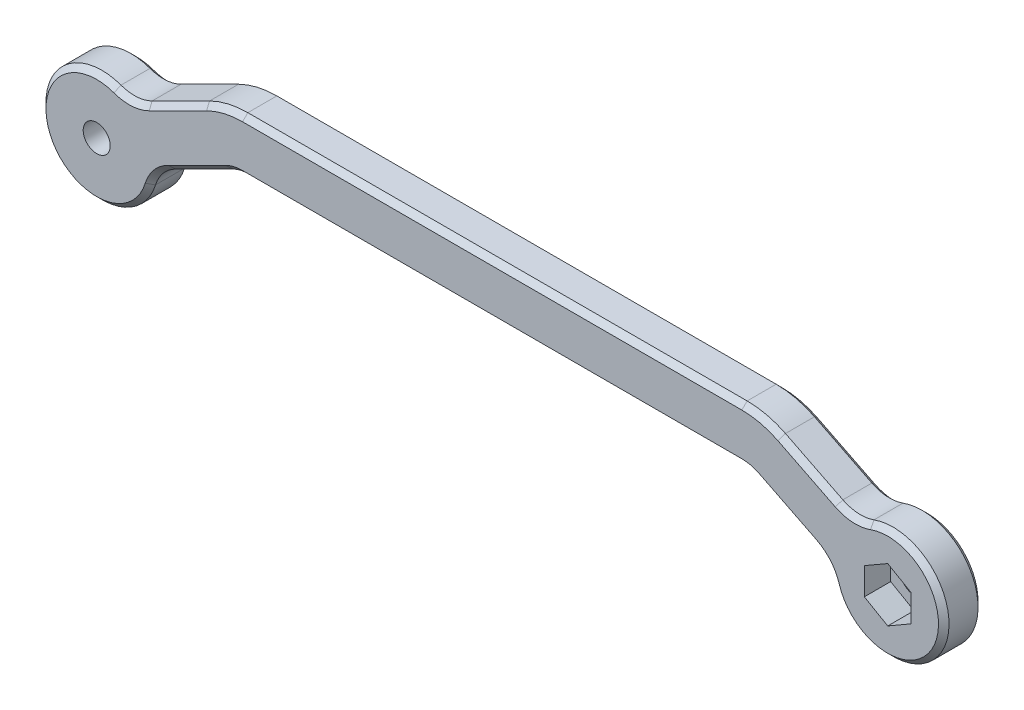
SolidWorks part; units mm, degrees
ref_plane "Front Plane" through (0, 0, 0) normal (0, 0, 1) x (1, 0, 0)
ref_plane "Top Plane" through (0, 0, 0) normal (0, 1, 0) x (1, 0, 0)
ref_plane "Right Plane" through (0, 0, 0) normal (1, 0, 0) x (0, 0, -1)
sketch "Sketch1" plane through (0, 0, 0) normal (0, 0, 1) x (1, 0, 0)
  line L0 (-60, 0) -> (60, 0) construction
  line L1 (-60, 0) -> (-40, 10) construction
  line L2 (-40, 10) -> (40, 10) construction
  line L3 (40, 10) -> (60, 0) construction
  line L4 (-40.9443, 14) -> (40.9443, 14) construction
  line L5 (40.9443, 14) -> (61.7889, 3.5777) construction
  line L6 (-61.7889, 3.5777) -> (-40.9443, 14) construction
  line L7 (-52.3974, 8.2735) -> (-43.6892, 12.6276)
  line L8 (-37.8754, 14) -> (37.8754, 14)
  line L9 (43.6892, 12.6276) -> (52.3974, 8.2735)
  line L10 (43.6892, 12.6276) -> (61.7889, 3.5777) construction
  line L11 (-37.8754, 6) -> (37.8754, 6)
  line L12 (40.1115, 5.4721) -> (48.8197, 1.118)
  line L13 (-61.7889, 3.5777) -> (-43.6892, 12.6276) construction
  line L14 (-48.8197, 1.118) -> (-40.1115, 5.4721)
  line L15 (-58.2111, -3.5777) -> (-40.1115, 5.4721) construction
  line L17 (40.1115, 5.4721) -> (58.2111, -3.5777) construction
  circle A0 centre (-60, 0) radius 2.05
  circle A1 centre (60, 0) radius 2.05
  arc A2 (-57.1162, 7.9959) -> (-51.873, -2.4905) centre (-60, 0) ccw
  arc A3 (51.873, -2.4905) -> (57.1162, 7.9959) centre (60, 0) ccw
  arc A4 (37.8754, 14) -> (43.6892, 12.6276) centre (37.8754, 1) cw
  arc A5 (-43.6892, 12.6276) -> (-37.8754, 14) centre (-37.8754, 1) cw
  arc A6 (-40.1115, 5.4721) -> (-37.8754, 6) centre (-37.8754, 1) cw
  arc A7 (37.8754, 6) -> (40.1115, 5.4721) centre (37.8754, 1) cw
  arc A8 (-52.3974, 8.2735) -> (-57.1162, 7.9959) centre (-55.0807, 13.64) cw
  arc A9 (52.3974, 8.2735) -> (57.1162, 7.9959) centre (55.0807, 13.64) ccw
  arc A10 (48.8197, 1.118) -> (51.873, -2.4905) centre (46.1364, -4.2485) cw
  arc A11 (-51.873, -2.4905) -> (-48.8197, 1.118) centre (-46.1364, -4.2485) cw
  point P4 (0, 0)
  point P9 (0, 10)
  dimension "D1" = 4.1
  dimension "D2" = 4.1
  dimension "D3" = 17
  dimension "D4" = 17
  dimension "D8" = 13
  dimension "D11" = 6
  dimension "D12" = 8
  dimension "D10" = 6
  dimension "D5" = 120
  dimension "D6" = 80
  dimension "D7" = 10
  dimension "D9" = 4
extrude "Boss-Extrude1" add sketch "Sketch1" along normal blind 6
sketch "Sketch3" plane through (0, 0, 6) normal (0, 0, 1) x (1, 0, 0)
  line L7 (60, 4.0992) -> (56.45, 2.0496)
  line L8 (56.45, 2.0496) -> (56.45, -2.0496)
  line L9 (56.45, -2.0496) -> (60, -4.0992)
  line L10 (60, -4.0992) -> (63.55, -2.0496)
  line L11 (63.55, -2.0496) -> (63.55, 2.0496)
  line L12 (63.55, 2.0496) -> (60, 4.0992)
  circle A3 centre (60, 0) radius 3.55 construction
  dimension "D2" = 7.1
extrude "Cut-Extrude1" cut sketch "Sketch3" against normal blind 4
chamfer "Chamfer3" distance 0.8 angle 45 32 edges at (39.0242, 5.8662, 0) (44.4656, 3.2951, 0) (0, 6, 0) (50.7167, -0.3729, 0) (-39.0242, 5.8662, 0) (67.6026, -3.8013, 0) (-44.4656, 3.2951, 0) (54.7283, 7.6504, 0) (-50.7167, -0.3729, 0) (48.0433, 10.4505, 0) (-67.6026, -3.8013, 0) (40.8622, 13.6522, 0) (-54.7283, 7.6504, 0) (0, 14, 0) (-48.0433, 10.4505, 0) (-40.8622, 13.6522, 0) (39.0242, 5.8662, 6) (44.4656, 3.2951, 6) (0, 6, 6) (50.7167, -0.3729, 6) (-39.0242, 5.8662, 6) (67.6026, -3.8013, 6) (-44.4656, 3.2951, 6) (54.7283, 7.6504, 6) (-50.7167, -0.3729, 6) (48.0433, 10.4505, 6) (-67.6026, -3.8013, 6) (40.8622, 13.6522, 6) (-54.7283, 7.6504, 6) (0, 14, 6) (-48.0433, 10.4505, 6) (-40.8622, 13.6522, 6)
